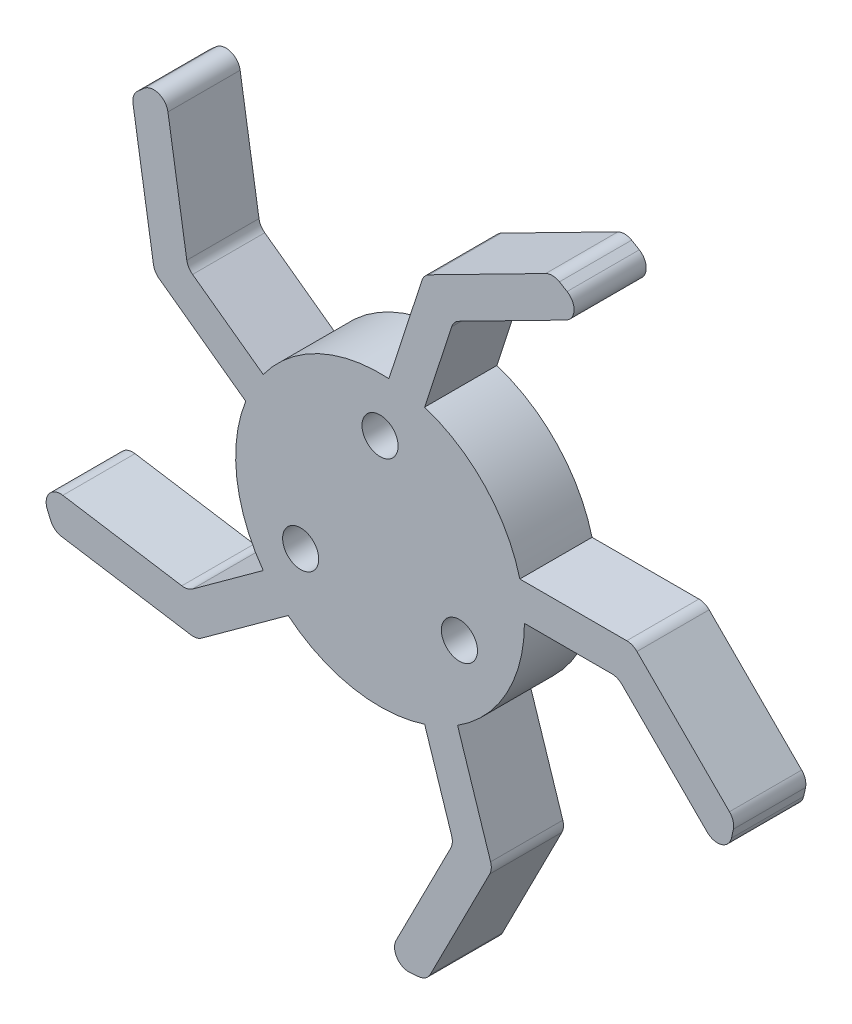
SolidWorks part; units mm, degrees
ref_plane "Front Plane" through (0, 0, 0) normal (0, 0, 1) x (1, 0, 0)
ref_plane "Top Plane" through (0, 0, 0) normal (0, 1, 0) x (1, 0, 0)
ref_plane "Right Plane" through (0, 0, 0) normal (1, 0, 0) x (0, 0, -1)
sketch "Sketch1" plane through (0, 0, 0) normal (0, 0, 1) x (1, 0, 0)
  circle A0 centre (0, 0) radius 25.4
  dimension "D1" = 50.8
extrude "Hub main" add sketch "Sketch1" along normal blind 12.7
sketch "Sketch2" plane through (0, 0, 12.7) normal (0, 0, 1) x (1, 0, 0)
  circle A0 centre (0, 15.875) radius 3.175
  point P2 (0, 0)
  dimension "D1" = 6.35
  dimension "D2" = 15.875
extrude "Hub bolt holes" cut sketch "Sketch2" against normal through all contours A0
pattern_circular "CirPattern1" count 3 over 360 about axis through (0, -0.252, 0) along (0, 0, 1) of "Hub bolt holes"
sketch "Sketch4" plane through (0, 0, 12.7) normal (0, 0, 1) x (1, 0, 0)
  line L0 (24.5934, 6.35) -> (44.45, 6.35)
  line L1 (44.45, 6.35) -> (62.4265, -11.6265)
  line L2 (25.4, 0) -> (41.8197, 0)
  line L3 (41.8197, 0) -> (60.6453, -18.8255)
  arc A0 (60.6453, -18.8255) -> (62.4265, -11.6265) centre (0, 0) ccw
  circle A1 centre (0, 0) radius 25.4 construction
  arc A2 (25.4, 0) -> (24.5934, 6.35) centre (0, 0) ccw
  dimension "D1" = 127
  dimension "D2" = 45
  dimension "D3" = 6.35
  dimension "D4" = 6.35
  dimension "D5" = 44.45
extrude "leg" add sketch "Sketch4" against normal blind 12.7 contours L3 A0 L1 L0 A2 L2
fillet "Fillet1" radius 2.54 4 edges at (44.45, 6.35, 6.35) (62.4265, -11.6265, 6.35) (60.6453, -18.8255, 6.35) (41.8197, 0, 6.35)
pattern_circular "CirPattern2" count 5 over 360 about axis through (0, 0, 0) along (0, 0, 1) of "Fillet1", "leg"
